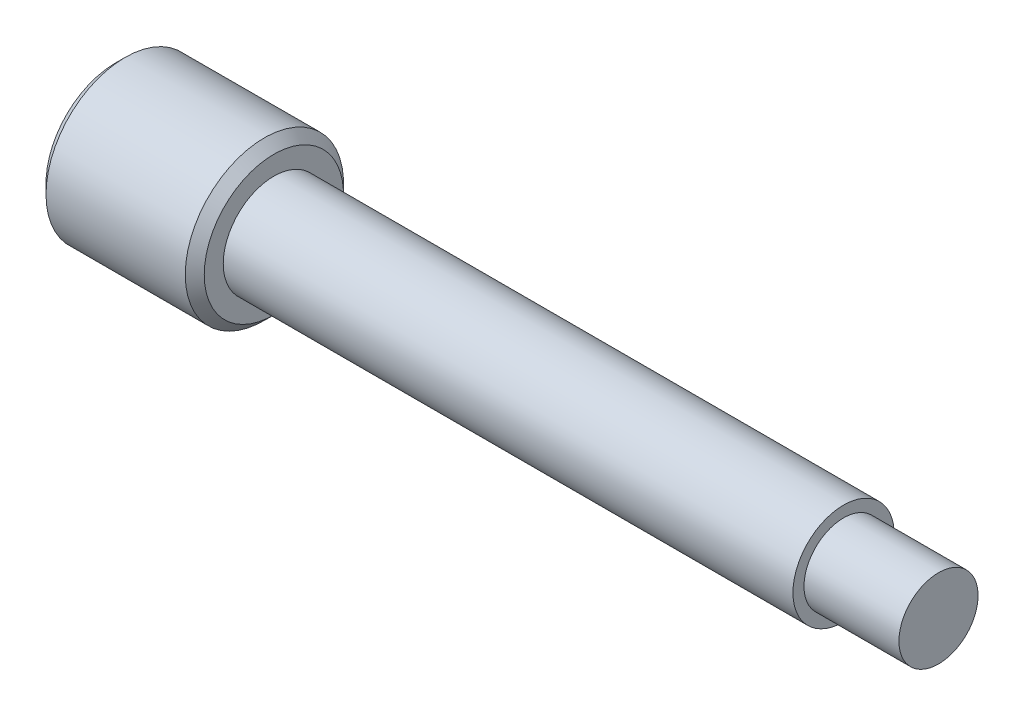
SolidWorks part; units mm, degrees
ref_plane "Front Plane" through (0, 0, 0) normal (0, 0, 1) x (1, 0, 0)
ref_plane "Top Plane" through (0, 0, 0) normal (0, 1, 0) x (1, 0, 0)
ref_plane "Right Plane" through (0, 0, 0) normal (1, 0, 0) x (0, 0, -1)
sketch "Sketch2" plane through (0, 0, 0) normal (0, 1, 0) x (1, 0, 0)
  line L0 (-6.1538, 0) -> (11.6084, 0) construction
  line L2 (-16.4965, 2.5) -> (-11.4965, 2.5)
  line L3 (-11.4965, 2.5) -> (-11.4965, 1.6)
  line L4 (-11.4965, 1.6) -> (6.5035, 1.6)
  line L5 (6.5035, 1.6) -> (6.5035, 1.25)
  line L6 (6.5035, 1.25) -> (9.5035, 1.25)
  line L7 (9.5035, 1.25) -> (9.5035, 0)
  line L8 (9.5035, 0) -> (-16.4965, 0)
  line L9 (-16.4965, 0) -> (-16.4965, 2.5)
  point P3 (-13.9965, 2.5)
  dimension "D1" = 1.25
  dimension "D2" = 1.6
  dimension "D3" = 2.5
  dimension "D4" = 5
  dimension "D5" = 18
  dimension "D6" = 3
revolve "Revolve1" add sketch "Sketch2" angle 360 about L0
chamfer "Chamfer1" distance 0.3 angle 45 2 edges at (-11.4965, 0, 2.5) (-16.4965, 0, 2.5)
